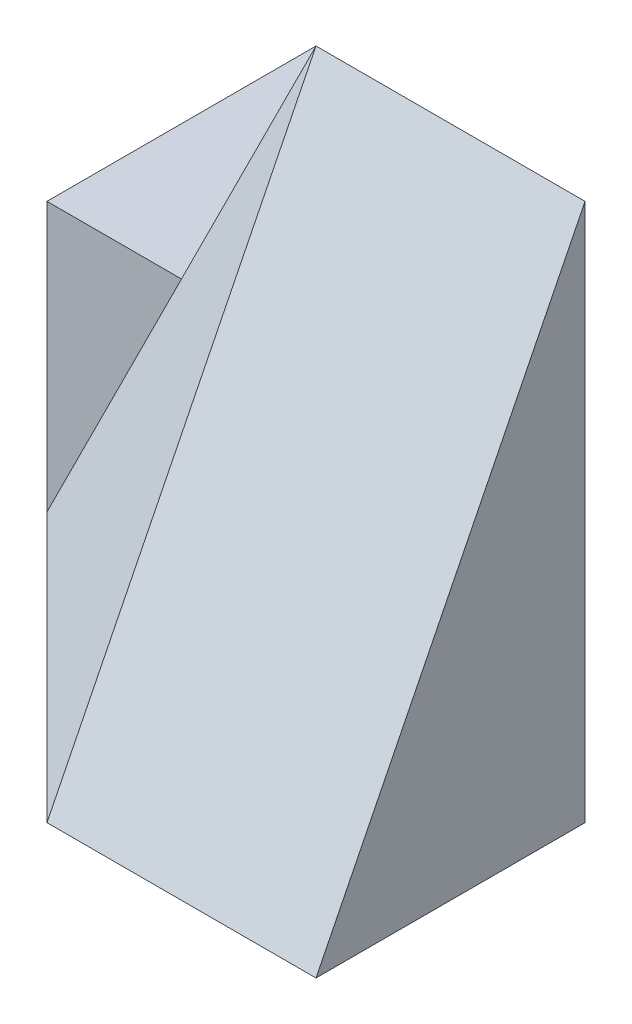
SolidWorks part; units mm, degrees
ref_plane "Front Plane" through (0, 0, 0) normal (0, 0, 1) x (1, 0, 0)
ref_plane "Top Plane" through (0, 0, 0) normal (0, 1, 0) x (1, 0, 0)
ref_plane "Right Plane" through (0, 0, 0) normal (1, 0, 0) x (0, 0, -1)
sketch "Sketch1" plane through (0, 0, 0) normal (0, 0, 1) x (1, 0, 0)
  line L1 (0, 0) -> (40, 0)
  line L2 (0, 0) -> (0, 20)
  line L3 (0, 20) -> (40, 20)
  line L4 (40, 0) -> (40, 20)
  dimension "D1" = 40
  dimension "D2" = 20
extrude "Boss-Extrude1" add sketch "Sketch1" along normal blind 40
sketch "Sketch2" plane through (0, 20, 0) normal (0, 1, 0) x (1, 0, 0)
  line L0 (0, -20) -> (20, -40)
  line L1 (0, -40) -> (0, 0) construction
  line L2 (40, -40) -> (0, -40) construction
  line L3 (20, -40) -> (0, -40)
  line L4 (0, -40) -> (0, -20)
extrude "Cut-Extrude1" cut sketch "Sketch2" against normal blind 40
sketch "Sketch3" plane through (0, 20, 0) normal (0, 1, 0) x (1, 0, 0)
  line L0 (0, -20) -> (20, -20)
  line L1 (20, -40) -> (20, -20)
  line L2 (0, -20) -> (20, -40)
  line L3 (0, -20) -> (20, -40)
  line M2 (0, -20) -> (20, -40)
extrude "Cut-Extrude2" cut sketch "Sketch3" against normal blind 40 contours L1 L0 M2
sketch "Sketch4" plane through (0, 20, 0) normal (0, 1, 0) x (1, 0, 0)
  line L0 (0, 0) -> (0, -20)
  line L1 (0, -20) -> (40, -20)
  line L2 (40, -40) -> (40, 0) construction
  line L3 (40, -20) -> (20, 0)
  line L4 (40, 0) -> (0, 0) construction
  line L5 (20, 0) -> (0, 0)
extrude "Boss-Extrude2" add sketch "Sketch4" along normal blind 20
ref_plane "Plane1" through (-8.8889, 4.4444, 8.8889) normal (-0.6667, 0.3333, 0.6667) x (0.7454, 0.2981, 0.5963)
sketch "Sketch5" plane through (-8.8889, 4.4444, 8.8889) normal (-0.6667, 0.3333, 0.6667) x (0.7454, 0.2981, 0.5963)
  line L0 (11.9257, -8.9443) -> (38.7585, -17.8885)
  line L1 (38.7585, -17.8885) -> (38.7585, 26.8328)
  line L2 (23.8514, 26.8328) -> (53.6656, 26.8328) construction
  line L3 (38.7585, 26.8328) -> (11.9257, -8.9443)
extrude "Boss-Extrude3" add sketch "Sketch5" against normal blind 20
sketch "Sketch6" plane through (0, 0, 0) normal (0, -1, 0) x (1, 0, 0)
  line L1 (40, 0) -> (0, 0)
  line L2 (40, 0) -> (40, 40)
  line L3 (40, 40) -> (0, 40)
  line L4 (0, 0) -> (0, 40)
  dimension "D1" = 40
  dimension "D2" = 40
extrude "Cut-Extrude3" cut sketch "Sketch6" along normal blind 20
sketch "Sketch7" plane through (10, 0, -10) normal (0.7071, 0, -0.7071) x (-0.7071, 0, -0.7071)
  line L1 (-42.4264, 40) -> (-14.1421, 40)
  line L2 (-42.4264, 40) -> (-42.4264, 20)
  line L3 (-42.4264, 20) -> (-14.1421, 20)
  line L4 (-14.1421, 40) -> (-14.1421, 20)
extrude "Cut-Extrude4" cut sketch "Sketch7" along normal blind 20
ref_plane "Plane2" through (20, 0, 0) normal (1, 0, 0) x (0, 0, -1)
sketch "Sketch8" plane through (20, 0, 0) normal (1, 0, 0) x (0, 0, -1)
  line L1 (-40, 20) -> (-20, 20)
  line L2 (-40, 20) -> (-40, 40)
  line L3 (-40, 40) -> (-20, 40)
  line L4 (-20, 20) -> (-20, 40)
extrude "Cut-Extrude5" cut sketch "Sketch8" along normal blind 20
sketch "Sketch9" plane through (0, 0, 20) normal (0, 0, 1) x (1, 0, 0)
  line L0 (0, 20) -> (10, 20)
  line L1 (0, 0) -> (0, 40) construction
  line L2 (20, 40) -> (0, 0) construction
  line L3 (10, 20) -> (20, 40)
  line L4 (0, 40) -> (20, 40) construction
  line L5 (20, 40) -> (0, 40)
  line L6 (0, 40) -> (0, 20)
  line L7 (0, 40) -> (0, 20)
  line M1 (0, 0) -> (20, 40)
  line M2 (20, 40) -> (0, 40)
  line M3 (0, 40) -> (0, 0)
extrude "Cut-Extrude6" cut sketch "Sketch9" against normal blind 20 contours L0 M3 M1 M2
sketch "Sketch10" plane through (0, 20, 0) normal (0, 1, 0) x (1, 0, 0)
  line L0 (40, 0) -> (40, -20)
  line L1 (40, -20) -> (20, 0)
  line L2 (40, -20) -> (20, 0) construction
  line L3 (40, 0) -> (20, 0) construction
  line L4 (20, 0) -> (40, 0)
extrude "Cut-Extrude7" cut sketch "Sketch10" against normal blind 20
sketch "Sketch11" plane through (0, 0, 20) normal (0, 0, 1) x (1, 0, 0)
  line L1 (20, 40) -> (40, 40)
  line L2 (20, 40) -> (20, 20)
  line L3 (20, 20) -> (40, 20)
  line L4 (40, 40) -> (40, 20)
extrude "Cut-Extrude8" cut sketch "Sketch11" against normal blind 20
sketch "Sketch12" plane through (0, 0, 40) normal (0, 0, 1) x (1, 0, 0)
  line L1 (20, 20) -> (40, 20)
  line L2 (20, 20) -> (20, 40)
  line L3 (20, 40) -> (40, 40)
  line L4 (40, 20) -> (40, 40)
  dimension "D1" = 20
  dimension "D2" = 20
extrude "Boss-Extrude4" add sketch "Sketch12" against normal blind 20
sketch "Sketch14" plane through (20, 0, 0) normal (1, 0, 0) x (0, 0, -1)
  line L0 (-20, 20) -> (0, 40)
  line L1 (0, 40) -> (-20, 40)
  line L2 (-20, 40) -> (-20, 20)
  line L3 (0, 40) -> (0, 20)
  line L4 (0, 20) -> (-20, 20)
  line L5 (-20, 40) -> (0, 20)
  line M1 (0, 40) -> (-20, 40)
  line M4 (0, 20) -> (0, 40)
extrude "Cut-Extrude9" cut sketch "Sketch14" against normal blind 20 contours L5 L0 M1 | L0 L5 M4
sketch "Sketch15" plane through (20, 0, 0) normal (-1, 0, 0) x (0, 0, 1)
  line L0 (20, 40) -> (40, 0)
  line L1 (40, 0) -> (40, 40)
  line L2 (40, 40) -> (20, 40)
extrude "Cut-Extrude10" cut sketch "Sketch15" against normal blind 20
